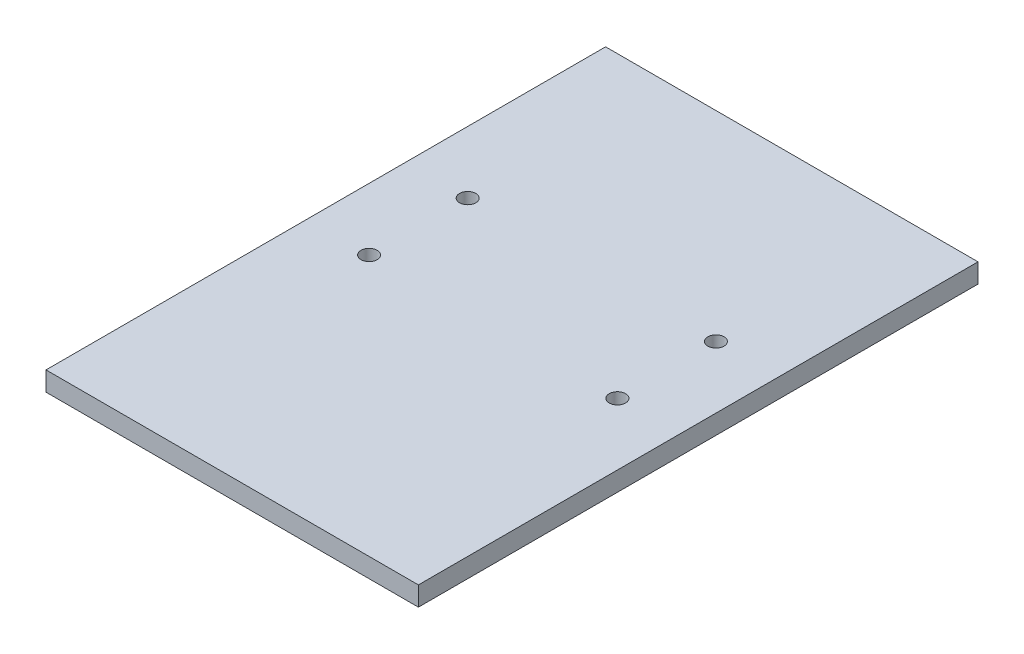
SolidWorks part; units mm, degrees
other "Markup1"
sketch "Sketch5" plane through (-120.015, 12.7, 180.34) normal (-0.0435, 0.9946, 0.0939) x (0.9888, 0.0294, 0.1461)
ref_plane "Front Plane" through (0, 0, 0) normal (0, 0, 1) x (1, 0, 0)
ref_plane "Top Plane" through (0, 0, 0) normal (0, 1, 0) x (1, 0, 0)
ref_plane "Right Plane" through (0, 0, 0) normal (1, 0, 0) x (0, 0, -1)
other "Center of Mass"
sketch "Sketch1" plane through (0, 0, 0) normal (0, 1, 0) x (1, 0, 0)
  line L1 (-120.015, 180.34) -> (120.015, 180.34)
  line L2 (-120.015, 180.34) -> (-120.015, -180.34)
  line L3 (-120.015, -180.34) -> (120.015, -180.34)
  line L4 (120.015, 180.34) -> (120.015, -180.34)
  line L5 (-120.015, 180.34) -> (120.015, -180.34) construction
  line L6 (-120.015, -180.34) -> (120.015, 180.34) construction
  point P0 (0, 0)
extrude "Boss-Extrude1" add sketch "Sketch1" along normal blind 12.446
sketch "Sketch2" plane through (0, 12.446, 0) normal (0, 1, 0) x (1, 0, 0)
  line L1 (-120.015, 180.34) -> (120.015, 180.34)
  line L2 (-120.015, 180.34) -> (-120.015, -180.34)
  line L3 (-120.015, -180.34) -> (120.015, -180.34)
  line L4 (120.015, 180.34) -> (120.015, -180.34)
  line L5 (-120.015, 180.34) -> (120.015, -180.34) construction
  line L6 (-120.015, -180.34) -> (120.015, 180.34) construction
  line L11 (67.31, 76.835) -> (92.71, 76.835)
  line L12 (67.31, 76.835) -> (67.31, -180.34)
  line L13 (67.31, -180.34) -> (92.71, -180.34)
  line L14 (92.71, 76.835) -> (92.71, -180.34)
  line L15 (67.31, 76.835) -> (92.71, -180.34) construction
  line L16 (67.31, -180.34) -> (92.71, 76.835) construction
  circle A0 centre (80.01, 51.435) radius 2.54
  circle A1 centre (80.01, -12.065) radius 2.54
  point P0 (0, 0)
  point P7 (80.01, -51.7525)
  dimension "D2" = 63.5
  dimension "D1" = 80.01
  dimension "D3" = 25.4
hole_wizard "Tap Drill for M10 Helicoil1" positions "Sketch3" profile "Sketch4" hole size "M10x1.5" standard "ANSI Metric"
sketch "Sketch3" plane through (0, 12.446, 0) normal (0, 1, 0) x (1, 0, 0)
  point P0 (80.01, 51.435)
  point P3 (80.01, -12.065)
sketch "Sketch4" plane through (80.01, 12.446, -51.435) normal (1, 0, 0) x (0, 0, 1)
  line L0 (0, 0) -> (0, 28.1545)
  line L1 (0, 28.1545) -> (5.25, 25)
  line L2 (5.25, 25) -> (5.25, 0)
  line L5 (5.25, 0) -> (0, 0)
  line L10 (0, 28.1545) -> (-5.25, 25) construction
  line L11 (0, -6.35) -> (0, 107.95) construction
  dimension "Hole Dia." = 10.5
  dimension "Hole Depth" = 25
  dimension "Drill Angle" = 118
ref_plane "Plane1" through (0, 0, 0) normal (-1, 0, 0) x (0, 0, 1)
mirror "Mirror1" about plane through (0, 0, 0) normal (-1, 0, 0) of "Tap Drill for M10 Helicoil1"
